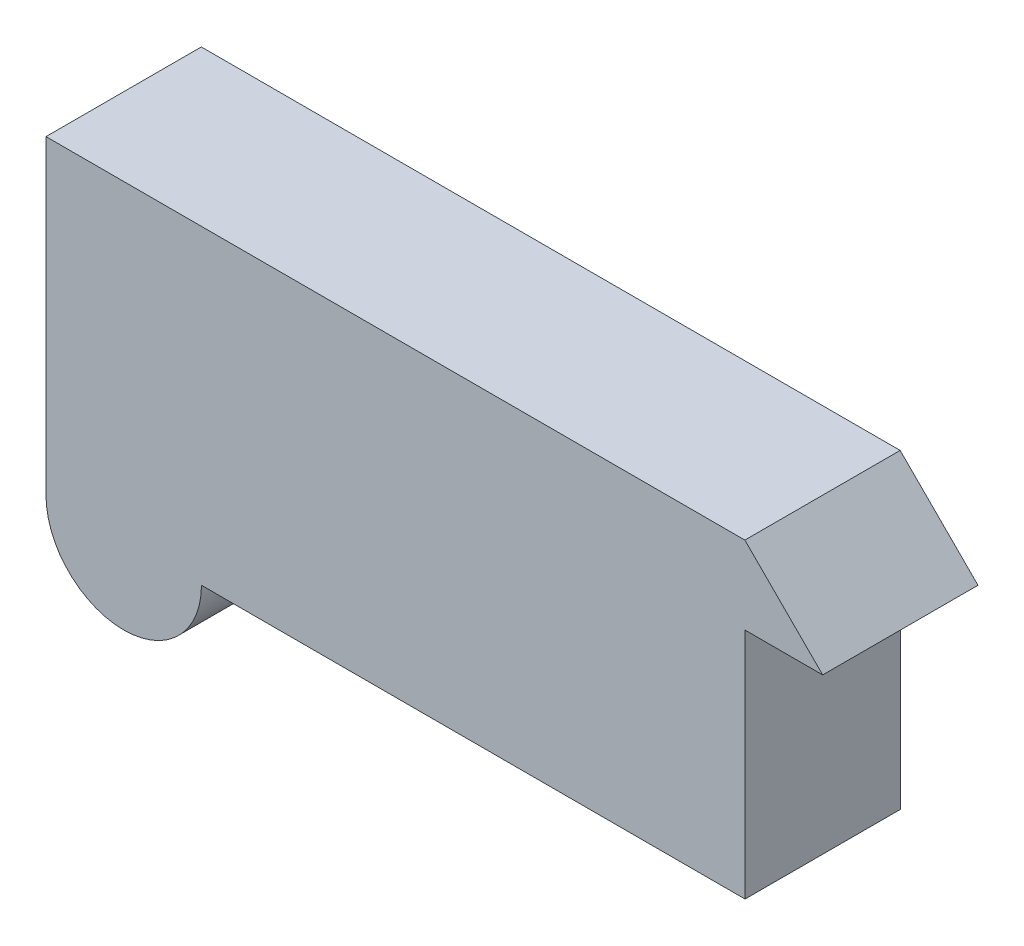
SolidWorks part; units mm, degrees
ref_plane "Front Plane" through (0, 0, 0) normal (0, 0, 1) x (1, 0, 0)
ref_plane "Top Plane" through (0, 0, 0) normal (0, 1, 0) x (1, 0, 0)
ref_plane "Right Plane" through (0, 0, 0) normal (1, 0, 0) x (0, 0, -1)
sketch "Sketch1" plane through (0, 0, 0) normal (0, 0, 1) x (1, 0, 0)
  line L0 (-1664.5392, 1529.8615) -> (621.4608, 1529.8615)
  line L1 (621.4608, 1529.8615) -> (876.094, 1275.2283)
  line L2 (876.094, 1275.2283) -> (622.094, 1275.2283)
  line L3 (622.094, 1275.2283) -> (622.094, 513.2283)
  line L4 (622.094, 513.2283) -> (-1155.906, 513.2283)
  line L5 (-1664.5392, 1529.8615) -> (-1664.5392, 513.8615)
  line L12 (622.094, 1275.2283) -> (876.094, 1275.2283) construction
  arc A2 (-1664.5392, 513.8615) -> (-1155.906, 513.2283) centre (-1410.2226, 513.5449) ccw
  dimension "D3" = 1778
  dimension "D1" = 2286
  dimension "D2" = 1016
  dimension "D5" = 254
  dimension "D6" = 762
extrude "Boss-Extrude1" add sketch "Sketch1" along normal blind 508
